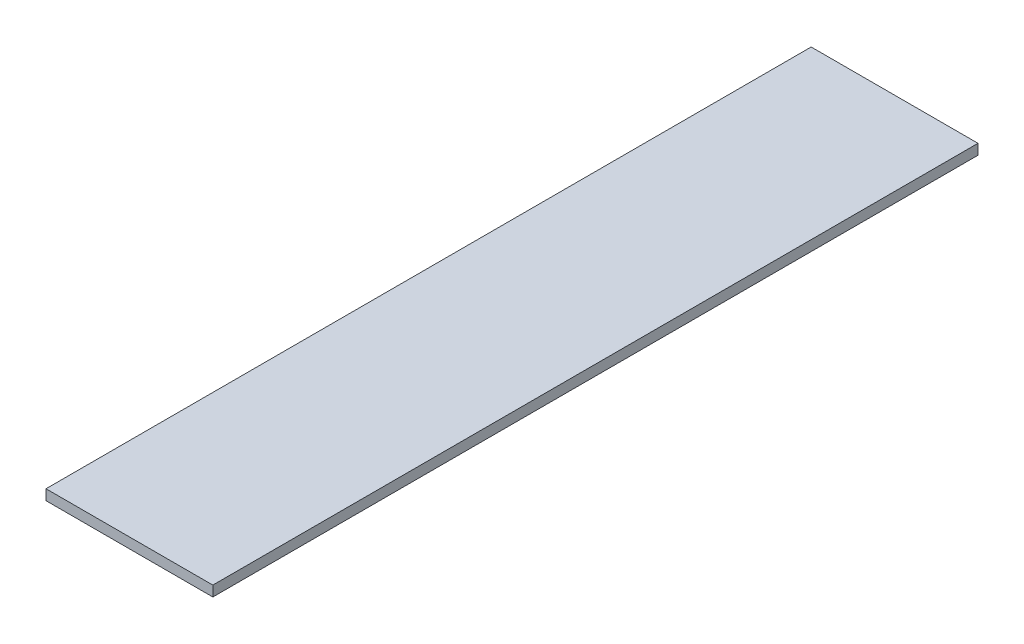
SolidWorks part; units mm, degrees
material "6061-O (SS)"
ref_plane "Front Plane" through (0, 0, 0) normal (0, 0, 1) x (1, 0, 0)
ref_plane "Top Plane" through (0, 0, 0) normal (0, 1, 0) x (1, 0, 0)
ref_plane "Right Plane" through (0, 0, 0) normal (1, 0, 0) x (0, 0, -1)
sketch "Sketch1" plane through (0, 0, 0) normal (0, 1, 0) x (1, 0, 0)
  line L1 (0, 0) -> (102.3, 0)
  line L2 (0, 0) -> (0, 469.2)
  line L3 (0, 469.2) -> (102.3, 469.2)
  line L4 (102.3, 0) -> (102.3, 469.2)
  dimension "D1" = 469.2
  dimension "D2" = 102.3
extrude "Boss-Extrude1" add sketch "Sketch1" along normal blind 6.35
